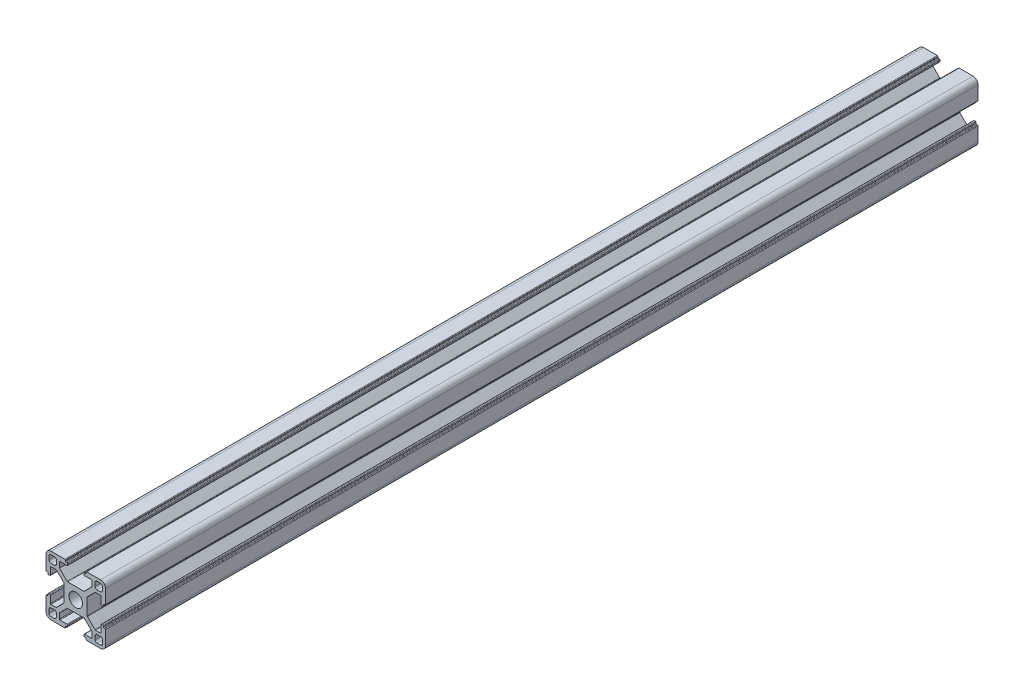
SolidWorks part; units mm, degrees
ref_plane "前视基准面" through (0, 0, 0) normal (0, 0, 1) x (1, 0, 0)
ref_plane "上视基准面" through (0, 0, 0) normal (0, 1, 0) x (1, 0, 0)
ref_plane "右视基准面" through (0, 0, 0) normal (1, 0, 0) x (0, 0, -1)
sketch "Model" plane through (0, 0, 0) normal (0, 0, 1) x (1, 0, 0)
  line L0 (113.2252, 61.8821) -> (113.2252, 60.1321)
  line L1 (112.2252, 59.1321) -> (110.4752, 59.1321)
  line L2 (109.4752, 60.1321) -> (109.4752, 61.8821)
  line L3 (110.4752, 62.8821) -> (112.2252, 62.8821)
  line L4 (112.2252, 35.8821) -> (110.4752, 35.8821)
  line L5 (109.4752, 36.8821) -> (109.4752, 38.6321)
  line L6 (110.4752, 39.6321) -> (112.2252, 39.6321)
  line L7 (113.2252, 38.6321) -> (113.2252, 36.8821)
  line L8 (132.7252, 36.8821) -> (132.7252, 38.6321)
  line L9 (133.7252, 39.6321) -> (135.4752, 39.6321)
  line L10 (136.4752, 38.6321) -> (136.4752, 36.8821)
  line L11 (135.4752, 35.8821) -> (133.7252, 35.8821)
  line L12 (133.7252, 62.8821) -> (135.4752, 62.8821)
  line L13 (136.4752, 61.8821) -> (136.4752, 60.1321)
  line L14 (135.4752, 59.1321) -> (133.7252, 59.1321)
  line L15 (132.7252, 60.1321) -> (132.7252, 61.8821)
  line L16 (127.0953, 55.1821) -> (118.8551, 55.1821)
  line L17 (118.6429, 55.27) -> (114.813, 59.0999)
  line L18 (114.7252, 59.312) -> (114.7252, 61.8821)
  line L19 (115.0252, 62.1821) -> (118.5752, 62.1821)
  line L20 (118.8752, 62.4821) -> (118.8752, 63.0821)
  line L21 (118.5752, 63.3821) -> (118.0752, 63.3821)
  line L22 (117.7752, 63.6821) -> (117.7752, 64.0821)
  line L23 (117.4752, 64.3821) -> (110.4752, 64.3821)
  line L24 (107.9752, 61.8821) -> (107.9752, 54.8821)
  line L25 (108.2752, 54.5821) -> (108.6752, 54.5821)
  line L26 (108.9752, 54.2821) -> (108.9752, 53.7821)
  line L27 (109.2752, 53.4821) -> (109.8752, 53.4821)
  line L28 (110.1752, 53.7821) -> (110.1752, 57.3321)
  line L29 (110.4752, 57.6321) -> (113.0453, 57.6321)
  line L30 (113.2574, 57.5443) -> (117.0873, 53.7144)
  line L31 (117.1752, 53.5022) -> (117.1752, 45.262)
  line L32 (117.0873, 45.0499) -> (113.2574, 41.22)
  line L33 (113.0453, 41.1321) -> (110.4752, 41.1321)
  line L34 (110.1752, 41.4321) -> (110.1752, 44.9821)
  line L35 (109.8752, 45.2821) -> (109.2752, 45.2821)
  line L36 (108.9752, 44.9821) -> (108.9752, 44.4821)
  line L37 (108.6752, 44.1821) -> (108.2752, 44.1821)
  line L38 (107.9752, 43.8821) -> (107.9752, 36.8821)
  line L39 (110.4752, 34.3821) -> (117.4752, 34.3821)
  line L40 (117.7752, 34.6821) -> (117.7752, 35.0821)
  line L41 (118.0752, 35.3821) -> (118.5752, 35.3821)
  line L42 (118.8752, 35.6821) -> (118.8752, 36.2821)
  line L43 (118.5752, 36.5821) -> (115.0252, 36.5821)
  line L44 (114.7252, 36.8821) -> (114.7252, 39.4522)
  line L45 (114.813, 39.6644) -> (118.6429, 43.4943)
  line L46 (118.8551, 43.5821) -> (127.0953, 43.5821)
  line L47 (127.3074, 43.4943) -> (131.1373, 39.6644)
  line L48 (131.2252, 39.4522) -> (131.2252, 36.8821)
  line L49 (130.9252, 36.5821) -> (127.3752, 36.5821)
  line L50 (127.0752, 36.2821) -> (127.0752, 35.6821)
  line L51 (127.3752, 35.3821) -> (127.8752, 35.3821)
  line L52 (128.1752, 35.0821) -> (128.1752, 34.6821)
  line L53 (128.4752, 34.3821) -> (135.4752, 34.3821)
  line L54 (137.9752, 36.8821) -> (137.9752, 43.8821)
  line L55 (137.6752, 44.1821) -> (137.2752, 44.1821)
  line L56 (136.9752, 44.4821) -> (136.9752, 44.9821)
  line L57 (136.6752, 45.2821) -> (136.0752, 45.2821)
  line L58 (135.7752, 44.9821) -> (135.7752, 41.4321)
  line L59 (135.4752, 41.1321) -> (132.9051, 41.1321)
  line L60 (132.6929, 41.22) -> (128.863, 45.0499)
  line L61 (128.7752, 45.262) -> (128.7752, 53.5022)
  line L62 (128.863, 53.7144) -> (132.6929, 57.5443)
  line L63 (132.9051, 57.6321) -> (135.4752, 57.6321)
  line L64 (135.7752, 57.3321) -> (135.7752, 53.7821)
  line L65 (136.0752, 53.4821) -> (136.6752, 53.4821)
  line L66 (136.9752, 53.7821) -> (136.9752, 54.2821)
  line L67 (137.2752, 54.5821) -> (137.6752, 54.5821)
  line L68 (137.9752, 54.8821) -> (137.9752, 61.8821)
  line L69 (135.4752, 64.3821) -> (128.4752, 64.3821)
  line L70 (128.1752, 64.0821) -> (128.1752, 63.6821)
  line L71 (127.8752, 63.3821) -> (127.3752, 63.3821)
  line L72 (127.0752, 63.0821) -> (127.0752, 62.4821)
  line L73 (127.3752, 62.1821) -> (130.9252, 62.1821)
  line L74 (131.2252, 61.8821) -> (131.2252, 59.312)
  line L75 (131.1373, 59.0999) -> (127.3074, 55.27)
  arc A0 (113.2252, 61.8821) -> (112.2252, 62.8821) centre (112.2252, 61.8821) ccw
  arc A1 (112.2252, 59.1321) -> (113.2252, 60.1321) centre (112.2252, 60.1321) ccw
  arc A2 (109.4752, 60.1321) -> (110.4752, 59.1321) centre (110.4752, 60.1321) ccw
  arc A3 (110.4752, 62.8821) -> (109.4752, 61.8821) centre (110.4752, 61.8821) ccw
  arc A4 (112.2252, 35.8821) -> (113.2252, 36.8821) centre (112.2252, 36.8821) ccw
  arc A5 (109.4752, 36.8821) -> (110.4752, 35.8821) centre (110.4752, 36.8821) ccw
  arc A6 (110.4752, 39.6321) -> (109.4752, 38.6321) centre (110.4752, 38.6321) ccw
  arc A7 (113.2252, 38.6321) -> (112.2252, 39.6321) centre (112.2252, 38.6321) ccw
  arc A8 (132.7252, 36.8821) -> (133.7252, 35.8821) centre (133.7252, 36.8821) ccw
  arc A9 (133.7252, 39.6321) -> (132.7252, 38.6321) centre (133.7252, 38.6321) ccw
  arc A10 (136.4752, 38.6321) -> (135.4752, 39.6321) centre (135.4752, 38.6321) ccw
  arc A11 (135.4752, 35.8821) -> (136.4752, 36.8821) centre (135.4752, 36.8821) ccw
  circle A12 centre (122.9752, 49.3821) radius 3.4
  arc A13 (133.7252, 62.8821) -> (132.7252, 61.8821) centre (133.7252, 61.8821) ccw
  arc A14 (136.4752, 61.8821) -> (135.4752, 62.8821) centre (135.4752, 61.8821) ccw
  arc A15 (135.4752, 59.1321) -> (136.4752, 60.1321) centre (135.4752, 60.1321) ccw
  arc A16 (132.7252, 60.1321) -> (133.7252, 59.1321) centre (133.7252, 60.1321) ccw
  arc A17 (118.6429, 55.27) -> (118.8551, 55.1821) centre (118.8551, 55.4821) ccw
  arc A18 (114.7252, 59.312) -> (114.813, 59.0999) centre (115.0252, 59.312) ccw
  arc A19 (115.0252, 62.1821) -> (114.7252, 61.8821) centre (115.0252, 61.8821) ccw
  arc A20 (118.5752, 62.1821) -> (118.8752, 62.4821) centre (118.5752, 62.4821) ccw
  arc A21 (118.8752, 63.0821) -> (118.5752, 63.3821) centre (118.5752, 63.0821) ccw
  arc A22 (117.7752, 63.6821) -> (118.0752, 63.3821) centre (118.0752, 63.6821) ccw
  arc A23 (117.7752, 64.0821) -> (117.4752, 64.3821) centre (117.4752, 64.0821) ccw
  arc A24 (110.4752, 64.3821) -> (107.9752, 61.8821) centre (110.4752, 61.8821) ccw
  arc A25 (107.9752, 54.8821) -> (108.2752, 54.5821) centre (108.2752, 54.8821) ccw
  arc A26 (108.9752, 54.2821) -> (108.6752, 54.5821) centre (108.6752, 54.2821) ccw
  arc A27 (108.9752, 53.7821) -> (109.2752, 53.4821) centre (109.2752, 53.7821) ccw
  arc A28 (109.8752, 53.4821) -> (110.1752, 53.7821) centre (109.8752, 53.7821) ccw
  arc A29 (110.4752, 57.6321) -> (110.1752, 57.3321) centre (110.4752, 57.3321) ccw
  arc A30 (113.2574, 57.5443) -> (113.0453, 57.6321) centre (113.0453, 57.3321) ccw
  arc A31 (117.1752, 53.5022) -> (117.0873, 53.7144) centre (116.8752, 53.5022) ccw
  arc A32 (117.0873, 45.0499) -> (117.1752, 45.262) centre (116.8752, 45.262) ccw
  arc A33 (113.0453, 41.1321) -> (113.2574, 41.22) centre (113.0453, 41.4321) ccw
  arc A34 (110.1752, 41.4321) -> (110.4752, 41.1321) centre (110.4752, 41.4321) ccw
  arc A35 (110.1752, 44.9821) -> (109.8752, 45.2821) centre (109.8752, 44.9821) ccw
  arc A36 (109.2752, 45.2821) -> (108.9752, 44.9821) centre (109.2752, 44.9821) ccw
  arc A37 (108.6752, 44.1821) -> (108.9752, 44.4821) centre (108.6752, 44.4821) ccw
  arc A38 (108.2752, 44.1821) -> (107.9752, 43.8821) centre (108.2752, 43.8821) ccw
  arc A39 (107.9752, 36.8821) -> (110.4752, 34.3821) centre (110.4752, 36.8821) ccw
  arc A40 (117.4752, 34.3821) -> (117.7752, 34.6821) centre (117.4752, 34.6821) ccw
  arc A41 (118.0752, 35.3821) -> (117.7752, 35.0821) centre (118.0752, 35.0821) ccw
  arc A42 (118.5752, 35.3821) -> (118.8752, 35.6821) centre (118.5752, 35.6821) ccw
  arc A43 (118.8752, 36.2821) -> (118.5752, 36.5821) centre (118.5752, 36.2821) ccw
  arc A44 (114.7252, 36.8821) -> (115.0252, 36.5821) centre (115.0252, 36.8821) ccw
  arc A45 (114.813, 39.6644) -> (114.7252, 39.4522) centre (115.0252, 39.4522) ccw
  arc A46 (118.8551, 43.5821) -> (118.6429, 43.4943) centre (118.8551, 43.2821) ccw
  arc A47 (127.3074, 43.4943) -> (127.0953, 43.5821) centre (127.0953, 43.2821) ccw
  arc A48 (131.2252, 39.4522) -> (131.1373, 39.6644) centre (130.9252, 39.4522) ccw
  arc A49 (130.9252, 36.5821) -> (131.2252, 36.8821) centre (130.9252, 36.8821) ccw
  arc A50 (127.3752, 36.5821) -> (127.0752, 36.2821) centre (127.3752, 36.2821) ccw
  arc A51 (127.0752, 35.6821) -> (127.3752, 35.3821) centre (127.3752, 35.6821) ccw
  arc A52 (128.1752, 35.0821) -> (127.8752, 35.3821) centre (127.8752, 35.0821) ccw
  arc A53 (128.1752, 34.6821) -> (128.4752, 34.3821) centre (128.4752, 34.6821) ccw
  arc A54 (135.4752, 34.3821) -> (137.9752, 36.8821) centre (135.4752, 36.8821) ccw
  arc A55 (137.9752, 43.8821) -> (137.6752, 44.1821) centre (137.6752, 43.8821) ccw
  arc A56 (136.9752, 44.4821) -> (137.2752, 44.1821) centre (137.2752, 44.4821) ccw
  arc A57 (136.9752, 44.9821) -> (136.6752, 45.2821) centre (136.6752, 44.9821) ccw
  arc A58 (136.0752, 45.2821) -> (135.7752, 44.9821) centre (136.0752, 44.9821) ccw
  arc A59 (135.4752, 41.1321) -> (135.7752, 41.4321) centre (135.4752, 41.4321) ccw
  arc A60 (132.6929, 41.22) -> (132.9051, 41.1321) centre (132.9051, 41.4321) ccw
  arc A61 (128.7752, 45.262) -> (128.863, 45.0499) centre (129.0752, 45.262) ccw
  arc A62 (128.863, 53.7144) -> (128.7752, 53.5022) centre (129.0752, 53.5022) ccw
  arc A63 (132.9051, 57.6321) -> (132.6929, 57.5443) centre (132.9051, 57.3321) ccw
  arc A64 (135.7752, 57.3321) -> (135.4752, 57.6321) centre (135.4752, 57.3321) ccw
  arc A65 (135.7752, 53.7821) -> (136.0752, 53.4821) centre (136.0752, 53.7821) ccw
  arc A66 (136.6752, 53.4821) -> (136.9752, 53.7821) centre (136.6752, 53.7821) ccw
  arc A67 (137.2752, 54.5821) -> (136.9752, 54.2821) centre (137.2752, 54.2821) ccw
  arc A68 (137.6752, 54.5821) -> (137.9752, 54.8821) centre (137.6752, 54.8821) ccw
  arc A69 (137.9752, 61.8821) -> (135.4752, 64.3821) centre (135.4752, 61.8821) ccw
  arc A70 (128.4752, 64.3821) -> (128.1752, 64.0821) centre (128.4752, 64.0821) ccw
  arc A71 (127.8752, 63.3821) -> (128.1752, 63.6821) centre (127.8752, 63.6821) ccw
  arc A72 (127.3752, 63.3821) -> (127.0752, 63.0821) centre (127.3752, 63.0821) ccw
  arc A73 (127.0752, 62.4821) -> (127.3752, 62.1821) centre (127.3752, 62.4821) ccw
  arc A74 (131.2252, 61.8821) -> (130.9252, 62.1821) centre (130.9252, 61.8821) ccw
  arc A75 (131.1373, 59.0999) -> (131.2252, 59.312) centre (130.9252, 59.312) ccw
  arc A76 (127.0953, 55.1821) -> (127.3074, 55.27) centre (127.0953, 55.4821) ccw
extrude "凸台-拉伸1" add sketch "Model" along normal blind 440
